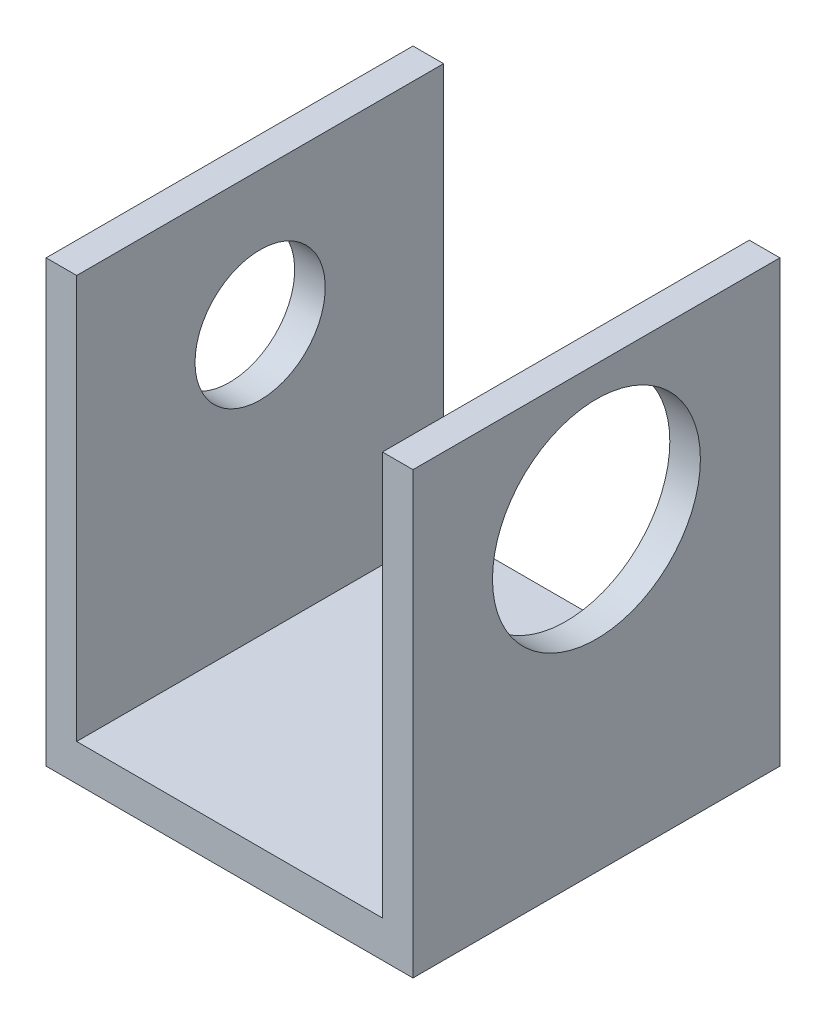
SolidWorks part; units mm, degrees
ref_plane "Front Plane" through (0, 0, 0) normal (0, 0, 1) x (1, 0, 0)
ref_plane "Top Plane" through (0, 0, 0) normal (0, 1, 0) x (1, 0, 0)
ref_plane "Right Plane" through (0, 0, 0) normal (1, 0, 0) x (0, 0, -1)
sketch "Sketch1" plane through (0, 0, 0) normal (0, 0, 1) x (1, 0, 0)
  line L0 (-3.3539, 6.8522) -> (-3.3539, -2.2918)
  line L1 (-3.3539, -2.2918) -> (4.2661, -2.2918)
  line L2 (4.2661, -2.2918) -> (4.2661, 6.8522)
  line L3 (3.6311, 6.8522) -> (3.6311, -1.5298)
  line L4 (3.6311, -1.5298) -> (-2.7189, -1.5298)
  line L5 (-2.7189, -1.5298) -> (-2.7189, 6.8522)
  line L6 (-2.7189, 6.8522) -> (-3.3539, 6.8522)
  line L7 (3.6311, 6.8522) -> (4.2661, 6.8522)
  dimension "D1" = 6.35
  dimension "D2" = 7.62
  dimension "D3" = 0.635
  dimension "D4" = 8.382
  dimension "D5" = 9.144
  dimension "D6" = 8.382
extrude "Boss-Extrude1" add sketch "Sketch1" along normal blind 7.62
sketch "Sketch2" plane through (-3.3539, 0, 0) normal (-1, 0, 0) x (0, 0, 1)
  line L0 (7.62, 6.8522) -> (0, 6.8522) construction
  line L1 (3.81, -2.2918) -> (3.81, 6.8522) construction
  point P0 (3.81, 4.0582)
  dimension "D1" = 2.794
hole_wizard "#6-32 Tapped Hole1" positions "Sketch3" profile "Sketch4" tap size "#6-32" standard "ANSI Inch" end condition up to next
sketch "Sketch3" plane through (-3.3539, 0, 0) normal (-1, 0, 0) x (0, 0, 1)
  point P0 (3.81, 4.0582)
sketch "Sketch4" plane through (-3.3539, 4.0582, 3.81) normal (0, 1, 0) x (0, 0, 1)
  line L0 (0, 0) -> (0, 0.635)
  line L1 (0, 0.635) -> (1.3525, 0.635)
  line L2 (1.3525, 0.635) -> (1.3525, 0)
  line L5 (1.3525, 0) -> (0, 0)
  line L11 (0, -6.35) -> (0, 107.95) construction
  dimension "Thread Major Dia." = 2.7051
  dimension "Thru Tap Drill Depth" = 0.635
sketch "Sketch5" plane through (4.2661, 0, 0) normal (1, 0, 0) x (0, 0, -1)
  point P0 (-3.81, 4.0582)
sketch "Sketch6" plane through (4.2661, 0, 0) normal (1, 0, 0) x (0, 0, -1)
  circle A0 centre (-3.81, 4.0582) radius 2.159
extrude "Cut-Extrude1" cut sketch "Sketch6" against normal up to next
sketch "Sketch12" plane through (-3.3539, 0, 0) normal (-1, 0, 0) x (0, 0, 1)
  line L0 (3.81, -2.2918) -> (3.81, 6.8522) construction
  line L1 (7.62, -2.2918) -> (0, -2.2918) construction
  line L2 (7.62, 6.8522) -> (0, 6.8522) construction
ref_plane "Plane1" through (0.508, 0, 0) normal (1, 0, 0) x (0, 0, -1)
